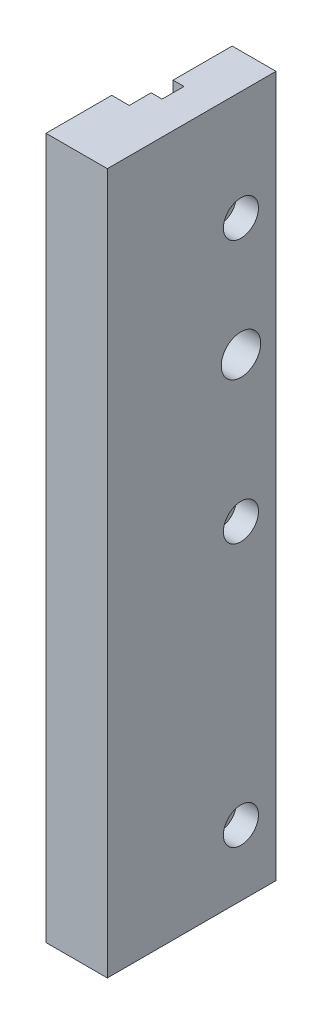
SolidWorks part; units mm, degrees
ref_plane "Front Plane" through (0, 0, 0) normal (0, 0, 1) x (1, 0, 0)
ref_plane "Top Plane" through (0, 0, 0) normal (0, 1, 0) x (1, 0, 0)
ref_plane "Right Plane" through (0, 0, 0) normal (1, 0, 0) x (0, 0, -1)
sketch "Sketch1" plane through (0, 0, 0) normal (0, 1, 0) x (1, 0, 0)
  line L1 (0, 20) -> (2.5, 20)
  line L2 (2.5, 20) -> (2.5, 25)
  line L3 (2.5, 25) -> (0, 25)
  line L4 (0, 25) -> (0, 38.5)
  line L5 (0, 38.5) -> (10, 38.5)
  line L6 (10, 38.5) -> (10, 0)
  line L7 (10, 0) -> (0, 0)
  line L8 (0, 20) -> (0, 15)
  line L9 (0, 15) -> (-4, 15)
  line L10 (-4, 15) -> (-4, 0)
  line L11 (-4, 0) -> (0, 0)
  dimension "D1" = 5
  dimension "D2" = 2.5
  dimension "D3" = 10
  dimension "D4" = 14
  dimension "D5" = 13.5
  dimension "D6" = 15
  dimension "D7" = 5
extrude "Boss-Extrude1" add sketch "Sketch1" along normal blind 160
sketch "Sketch2" plane through (10, 0, 0) normal (1, 0, 0) x (0, 0, -1)
  line L0 (38.5, 160) -> (38.5, 0) construction
  line L1 (0, 0) -> (38.5, 0) construction
  line L2 (0, 160) -> (38.5, 160) construction
  circle A0 centre (30.5, 15) radius 4
  circle A1 centre (30.5, 135) radius 4
  circle A2 centre (30.5, 75) radius 4
  circle A3 centre (30.5, 108) radius 4.5
  point P10 (0, 0)
  point P11 (32, 47.8309)
  point P12 (0, 0)
  point P13 (30.5, 11.0664)
  point P14 (30.5, 139.1853)
  point P15 (30.5, 116.0373)
  point P16 (30.5, 52)
  point P17 (30.5, 51.6343)
  dimension "D1" = 8
  dimension "D6" = 9
  dimension "D2" = 8
  dimension "D3" = 15
  dimension "D4" = 60
  dimension "D5" = 60
  dimension "D7" = 52
extrude "Cut-Extrude2" cut sketch "Sketch2" against normal blind 5
sketch "Sketch3" plane through (5, 0, 0) normal (1, 0, 0) x (0, 0, -1)
  circle A0 centre (30.5, 15) radius 2.5
  circle A1 centre (30.5, 135) radius 2.5
  circle A2 centre (30.5, 75) radius 2.5
  circle A3 centre (30.5, 108) radius 4.5
  dimension "D1" = 5
  dimension "D2" = 9
extrude "Cut-Extrude3" cut sketch "Sketch3" against normal through all
